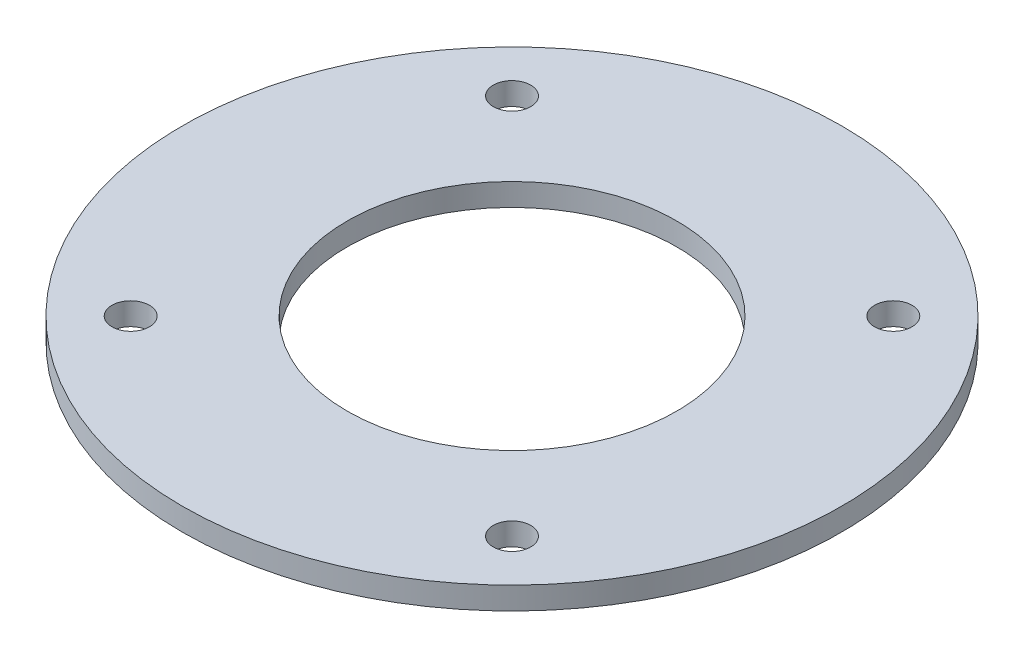
SolidWorks part; units mm, degrees
material "6061-T6 (SS)"
ref_plane "Front Plane" through (0, 0, 0) normal (0, 0, 1) x (1, 0, 0)
ref_plane "Top Plane" through (0, 0, 0) normal (0, 1, 0) x (1, 0, 0)
ref_plane "Right Plane" through (0, 0, 0) normal (1, 0, 0) x (0, 0, -1)
sketch "Sketch1" plane through (0, 0, 0) normal (0, 1, 0) x (1, 0, 0)
  line L0 (-131.5715, 173.4744) -> (-131.5715, 11.8298) construction
  line L5 (-131.5715, 11.8298) -> (30.0731, 11.8298) construction
  line L6 (30.0731, 11.8298) -> (30.0731, 173.4744) construction
  line L7 (30.0731, 173.4744) -> (-131.5715, 173.4744) construction
  circle A0 centre (-50.7492, 92.6521) radius 69.85
  circle A1 centre (-131.5715, 173.4744) radius 7.9375
  circle A2 centre (-131.5715, 11.8298) radius 7.9375
  circle A3 centre (30.0731, 11.8298) radius 7.9375
  circle A4 centre (30.0731, 173.4744) radius 7.9375
  circle A5 centre (-50.7492, 92.6521) radius 139.7
  point P1 (-50.7492, 173.4744)
  point P2 (30.0731, 92.6521)
  point P16 (-50.7492, 11.8298)
  point P18 (-131.5715, 92.6521)
  dimension "D1" = 279.4
  dimension "D2" = 139.7
  dimension "D3" = 15.875
  dimension "D4" = 15.875
  dimension "D5" = 15.875
  dimension "D7" = 15.875
  dimension "D6" = 228.6
extrude "Boss-Extrude1" add sketch "Sketch1" along normal blind 9.525 contours A5
sketch "Sketch2" plane through (0, 9.525, 0) normal (0, 1, 0) x (1, 0, 0)
  circle A0 centre (-131.5715, 173.4744) radius 19.8437
  circle A1 centre (30.0731, 173.4744) radius 19.8438
  circle A2 centre (30.0731, 11.8298) radius 19.8438
  circle A3 centre (-131.5715, 11.8298) radius 19.8437
  circle A4 centre (-131.5715, 173.4744) radius 7.9375
  circle A5 centre (-131.5715, 11.8298) radius 7.9375
  circle A6 centre (30.0731, 11.8298) radius 7.9375
  circle A7 centre (30.0731, 173.4744) radius 7.9375
  dimension "D5" = 15.875
  dimension "D7" = 15.875
  dimension "D1" = 39.6875
  dimension "D2" = 39.6875
  dimension "D3" = 39.6875
  dimension "D4" = 39.6875
  dimension "D6" = 15.875
  dimension "D8" = 15.875
equation "\"D3@Sketch1\"=\"thread_rod_size\""
equation "\"thread_rod_size\"= 5 / 8"
equation "\"D4@Sketch1\"=\"thread_rod_size\""
equation "\"D7@Sketch1\"=\"thread_rod_size\""
equation "\"D5@Sketch1\"=\"thread_rod_size\""
equation "\"D1@Sketch2\"=\"thread_rod_size\"*2.5"
equation "\"D2@Sketch2\"=\"thread_rod_size\"*2.5"
equation "\"D3@Sketch2\"=\"thread_rod_size\"*2.5"
equation "\"D4@Sketch2\"=\"thread_rod_size\"*2.5"
equation "\"D5@Sketch2\"=\"thread_rod_size\""
equation "\"D6@Sketch2\"=\"thread_rod_size\""
equation "\"D7@Sketch2\"=\"thread_rod_size\""
equation "\"D8@Sketch2\"=\"thread_rod_size\""
